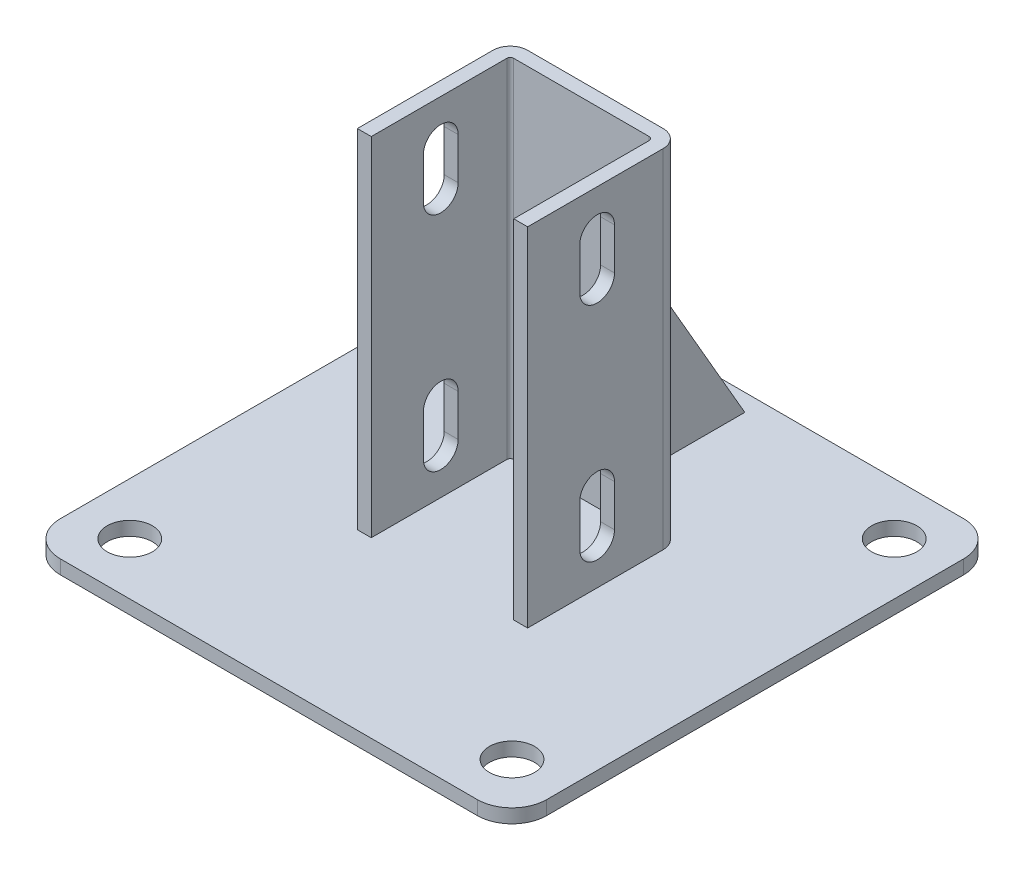
SolidWorks part; units mm, degrees
material "Ст3пс ГОСТ 380-2005"
ref_plane "Спереди" through (0, 0, 0) normal (0, 0, 1) x (1, 0, 0)
ref_plane "Сверху" through (0, 0, 0) normal (0, 1, 0) x (1, 0, 0)
ref_plane "Справа" through (0, 0, 0) normal (1, 0, 0) x (0, 0, -1)
sketch "Эскиз2" plane through (0, 0, 0) normal (0, 1, 0) x (1, 0, 0)
  line L1 (-70, -70) -> (70, -70)
  line L2 (-70, -70) -> (-70, 70)
  line L3 (-70, 70) -> (70, 70)
  line L4 (70, -70) -> (70, 70)
  line L5 (-70, -70) -> (70, 70) construction
  line L6 (-70, 70) -> (70, -70) construction
  point P0 (0, 0)
  dimension "D1" = 140
extrude "Бобышка-Вытянуть1" add sketch "Эскиз2" along normal blind 4
sketch "Эскиз3" plane through (0, 4, 0) normal (0, 1, 0) x (1, 0, 0)
  line L0 (-20.5, -20) -> (-20.5, 20)
  line L1 (-20.5, 20) -> (20.5, 20)
  line L2 (20.5, 20) -> (20.5, -20)
  point P2 (0, 20)
  point P5 (-20.5, 0)
  dimension "D2" = 41
  dimension "D3" = 40
extrude "Вытянуть-Тонкостенный1" add sketch "Эскиз3" along normal offset from surface (100 mm away) 104 thin up to face at (0, 0, 0) thin type one direction reverse wall 4
sketch "Эскиз4" plane through (0, 0, 0) normal (1, 0, 0) x (0, 0, -1)
  line L0 (24, 75.0141) -> (65, 4)
  line L1 (24, 104) -> (24, 4) construction
  line L2 (-70, 4) -> (70, 4) construction
  line L3 (65, 4) -> (24, 4)
  line L4 (24, 4) -> (24, 75.0141)
  line L5 (70, 4) -> (70, 0) construction
  dimension "D1" = 30
  dimension "D2" = 5
extrude "Бобышка-Вытянуть2" add sketch "Эскиз4" along normal mid plane 4
sketch "Эскиз5" plane through (24.5, 0, 0) normal (1, 0, 0) x (0, 0, -1)
  line L0 (0, 92) -> (0, 80) construction
  line L1 (5, 92) -> (5, 80)
  line L2 (-5, 92) -> (-5, 80)
  line L3 (0, 28) -> (0, 16) construction
  line L4 (5, 28) -> (5, 16)
  line L5 (-5, 28) -> (-5, 16)
  line L6 (-20, 104) -> (19, 104) construction
  line L7 (-70, 4) -> (70, 4) construction
  arc A0 (5, 92) -> (-5, 92) centre (0, 92) ccw
  arc A1 (-5, 80) -> (5, 80) centre (0, 80) ccw
  arc A2 (5, 28) -> (-5, 28) centre (0, 28) ccw
  arc A3 (-5, 16) -> (5, 16) centre (0, 16) ccw
  point P3 (0, 86)
  point P8 (0, 22)
  dimension "D2" = 12
  dimension "D4" = 12
  dimension "D1" = 10
  dimension "D3" = 12
extrude "Вырез-Вытянуть1" cut sketch "Эскиз5" against normal through all
sketch "Эскиз6" plane through (0, 4, 0) normal (0, 1, 0) x (1, 0, 0)
  line L0 (-70, 70) -> (-70, -70) construction
  line L1 (55, -55) -> (-55, -55) construction
  line L2 (55, -55) -> (55, 55) construction
  line L3 (55, 55) -> (-55, 55) construction
  line L4 (-55, -55) -> (-55, 55) construction
  line L5 (55, -55) -> (-55, 55) construction
  line L6 (55, 55) -> (-55, -55) construction
  line L7 (70, 70) -> (-70, 70) construction
  circle A0 centre (-55, 55) radius 6.5
  circle A1 centre (-55, -55) radius 6.5
  circle A2 centre (55, 55) radius 6.5
  circle A3 centre (55, -55) radius 6.5
  point P0 (0, 0)
  dimension "D1" = 13
  dimension "D2" = 15
  dimension "D3" = 15
extrude "Вырез-Вытянуть2" cut sketch "Эскиз6" against normal through all
fillet "Скругление1" radius 10 4 edges at (70, 2, 70) (-70, 2, 70) (-70, 2, -70) (70, 2, -70)
